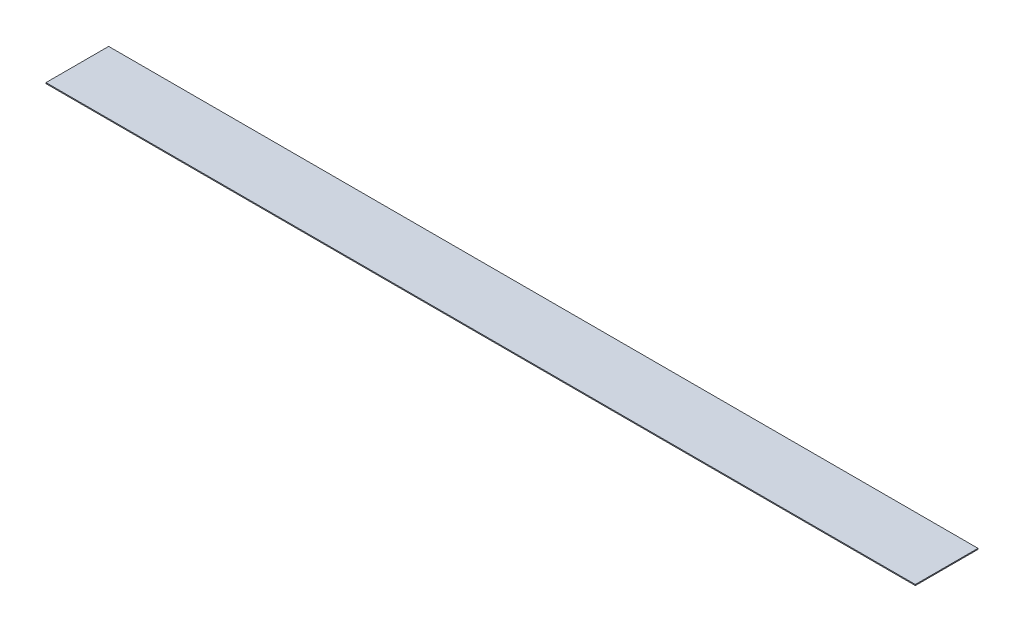
SolidWorks part; units mm, degrees
ref_plane "Front Plane" through (0, 0, 0) normal (0, 0, 1) x (1, 0, 0)
ref_plane "Top Plane" through (0, 0, 0) normal (0, 1, 0) x (1, 0, 0)
ref_plane "Right Plane" through (0, 0, 0) normal (1, 0, 0) x (0, 0, -1)
sketch "Sketch2" plane through (0, 0, 0) normal (0, 1, 0) x (1, 0, 0)
  line L1 (0, 0) -> (1409.7, 0)
  line L2 (0, 0) -> (0, -101.6)
  line L3 (0, -101.6) -> (1409.7, -101.6)
  line L4 (1409.7, 0) -> (1409.7, -101.6)
  dimension "D1" = 101.6
  dimension "D2" = 1409.7
extrude "Boss-Extrude1" add sketch "Sketch2" along normal blind 1.5875
